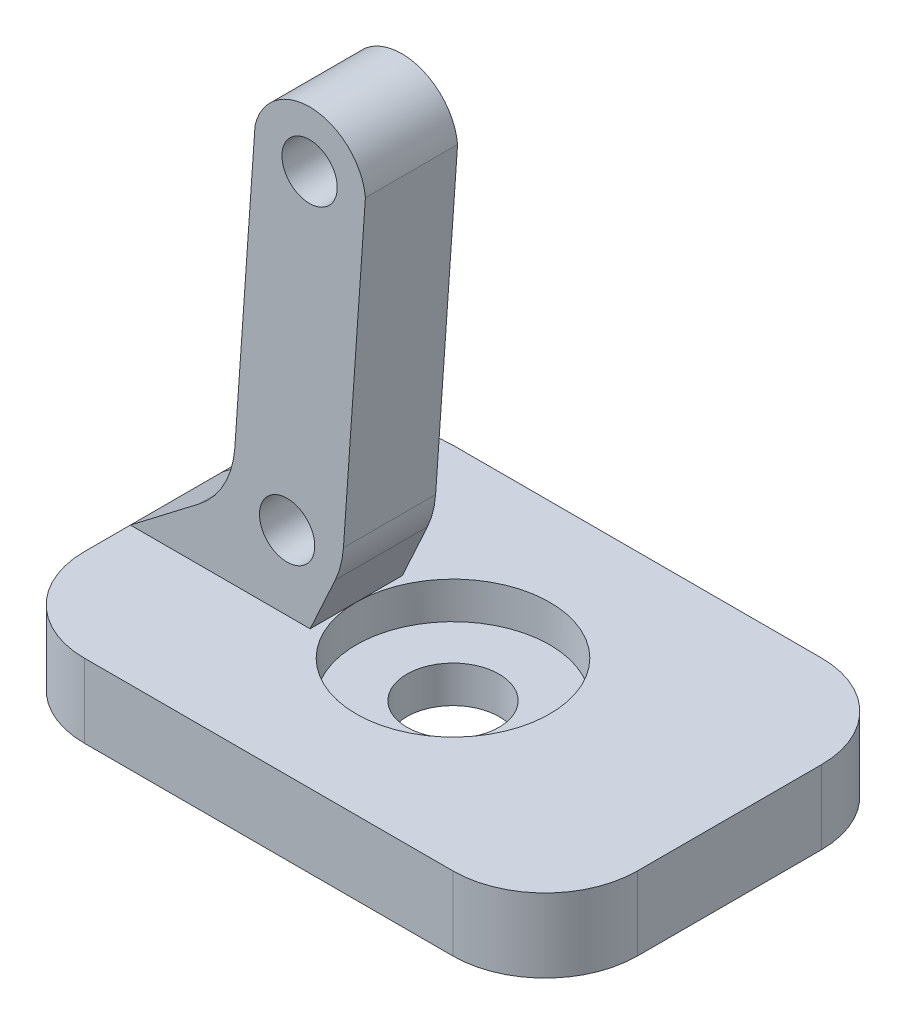
SolidWorks part; units mm, degrees
ref_plane "Front Plane" through (0, 0, 0) normal (0, 0, 1) x (1, 0, 0)
ref_plane "Top Plane" through (0, 0, 0) normal (0, 1, 0) x (1, 0, 0)
ref_plane "Right Plane" through (0, 0, 0) normal (1, 0, 0) x (0, 0, -1)
sketch "Sketch1" plane through (0, 0, 0) normal (0, 1, 0) x (1, 0, 0)
  line L1 (-15, 10) -> (15, 10)
  line L2 (-15, 10) -> (-15, -10)
  line L3 (-15, -10) -> (15, -10)
  line L4 (15, 10) -> (15, -10)
  line L5 (-15, 10) -> (15, -10) construction
  line L6 (-15, -10) -> (15, 10) construction
  point P0 (0, 0)
  dimension "D1" = 30
  dimension "D2" = 20
extrude "Boss-Extrude1" add sketch "Sketch1" along normal blind 4
sketch "Sketch2" plane through (0, 4, 0) normal (0, 1, 0) x (1, 0, 0)
  circle A0 centre (0, 0) radius 5.25
sketch "Sketch3" plane through (0, 4, 0) normal (0, 1, 0) x (1, 0, 0)
  circle A0 centre (0, 0) radius 2.5
extrude "Cut-Extrude1" cut sketch "Sketch2" against normal blind 2
extrude "Cut-Extrude2" cut sketch "Sketch3" against normal through all contours A0
sketch "Sketch4" plane through (0, 0, 0) normal (0, 0, 1) x (1, 0, 0)
  line L0 (-15, 4) -> (15, 4) construction
  line L1 (-15, 4) -> (-9.4927, 8.2188)
  line L2 (-15.728, 6.1487) -> (15, 4) construction
  line L3 (-6.6744, 5.5156) -> (-5.8195, 17.741) construction
  line L4 (-3.5073, 7.8003) -> (-5.25, 4)
  line L5 (-5.25, 4) -> (-15, 4)
  line L6 (-9.4927, 8.2188) -> (-8.2372, 26.1725)
  line L7 (-2.2519, 25.754) -> (-3.5073, 7.8003)
  line L8 (-9.4927, 8.2188) -> (-3.5073, 7.8003) construction
  circle A0 centre (-6.5, 8.0095) radius 1.5
  circle A1 centre (-5.2793, 25.4669) radius 1.5
  arc A2 (-8.2372, 26.1725) -> (-2.2519, 25.754) centre (-5.2793, 25.4669) cw
  dimension "D5" = 6
  dimension "D1" = 4
  dimension "D2" = 17.5
  dimension "D3" = 2.5
  dimension "D4" = 6.5
extrude "Boss-Extrude2" add sketch "Sketch4" along normal mid plane 5
fillet "Fillet1" radius 5 2 edges at (-3.5073, 7.8003, 0) (-9.4927, 8.2188, 0)
fillet "Fillet2" radius 5 4 edges at (15, 2, -10) (15, 2, 10) (-15, 2, -10) (-15, 2, 10)
